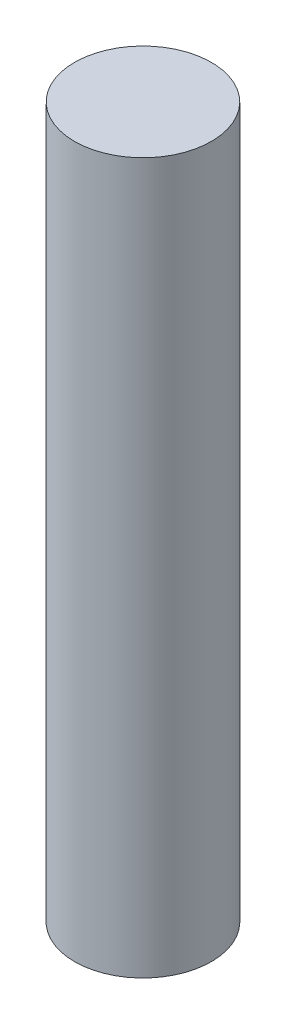
SolidWorks part; units mm, degrees
ref_plane "Front Plane" through (0, 0, 0) normal (0, 0, 1) x (1, 0, 0)
ref_plane "Top Plane" through (0, 0, 0) normal (0, 1, 0) x (1, 0, 0)
ref_plane "Right Plane" through (0, 0, 0) normal (1, 0, 0) x (0, 0, -1)
sketch "Sketch1" plane through (0, 0, 0) normal (0, 1, 0) x (1, 0, 0)
  circle A0 centre (0, 0) radius 4.3815
  dimension "D1" = 8.763
extrude "Boss-Extrude1" add sketch "Sketch1" along normal blind 45.466
